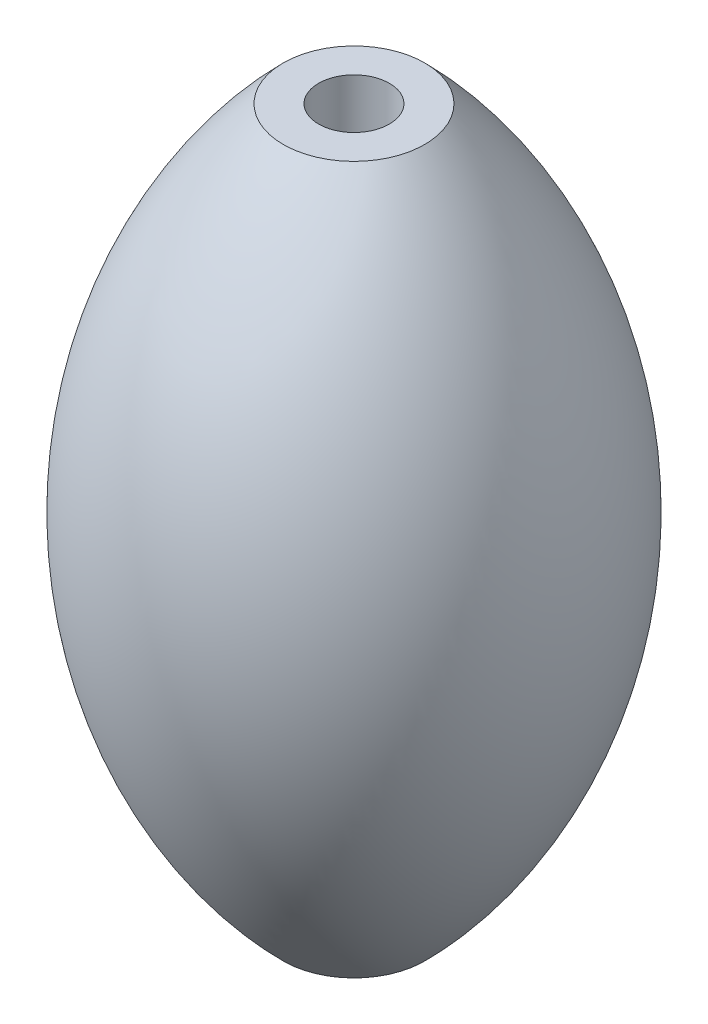
SolidWorks part; units mm, degrees
ref_plane "Front Plane" through (0, 0, 0) normal (0, 0, 1) x (1, 0, 0)
ref_plane "Top Plane" through (0, 0, 0) normal (0, 1, 0) x (1, 0, 0)
ref_plane "Right Plane" through (0, 0, 0) normal (1, 0, 0) x (0, 0, -1)
sketch "Sketch1" plane through (0, 0, 0) normal (0, 0, 1) x (1, 0, 0)
  line L0 (0, 5) -> (0, -5)
  line L1 (0, 5) -> (1, 5)
  line L2 (0, -5) -> (1, -5)
  arc A2 (1, 5) -> (1, -5) centre (-4, 0) cw
  point P3 (0, 0)
  dimension "D1" = 10
  dimension "D2" = 1
  dimension "D3" = 1
revolve "Revolve1" add sketch "Sketch1" angle 360 about L0
sketch "Sketch2" plane through (0, 5, 0) normal (0, 1, 0) x (1, 0, 0)
  circle A0 centre (0, 0) radius 0.5
extrude "Cut-Extrude1" cut sketch "Sketch2" against normal through all
